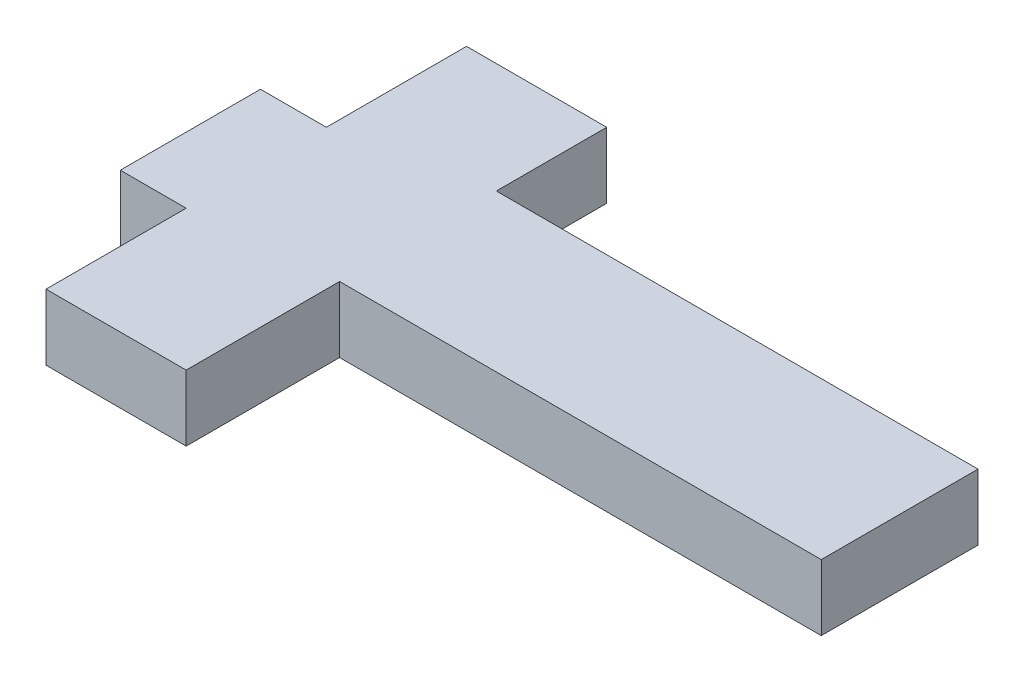
SolidWorks part; units mm, degrees
ref_plane "Front Plane" through (0, 0, 0) normal (0, 0, 1) x (1, 0, 0)
ref_plane "Top Plane" through (0, 0, 0) normal (0, 1, 0) x (1, 0, 0)
ref_plane "Right Plane" through (0, 0, 0) normal (1, 0, 0) x (0, 0, -1)
sketch "Sketch1" plane through (0, 0, 0) normal (0, 1, 0) x (1, 0, 0)
  line L12 (0, 0) -> (12.7, 0)
  line L13 (12.7, 0) -> (12.7, 13.9)
  line L14 (12.7, 13.9) -> (18.669, 13.9)
  line L15 (18.669, 13.9) -> (18.669, 28.1)
  line L16 (18.669, 28.1) -> (12.7, 28.1)
  line L17 (12.7, 28.1) -> (12.7, 38.1)
  line L18 (12.7, 38.1) -> (0, 38.1)
  line L19 (0, 38.1) -> (0, 25.4)
  line L20 (0, 25.4) -> (-5.969, 25.4)
  line L21 (-5.969, 25.4) -> (-5.969, 12.7)
  line L22 (-5.969, 12.7) -> (0, 12.7)
  line L23 (0, 12.7) -> (0, 0)
  dimension "D1" = 5.969
  dimension "D2" = 10
  dimension "D3" = 14.2
  dimension "D4" = 13.9
  dimension "D5" = 24.638
extrude "Boss-Extrude1" add sketch "Sketch1" along normal blind 5.969
sketch "Sketch2" plane through (0, 0, 0) normal (0, -1, 0) x (1, 0, 0)
  line L1 (18.669, -28.1) -> (56.338, -28.1)
  line L2 (18.669, -28.1) -> (18.669, -13.9)
  line L3 (18.669, -13.9) -> (56.338, -13.9)
  line L4 (56.338, -28.1) -> (56.338, -13.9)
  line L5 (18.669, -28.1) -> (56.338, -13.9) construction
  line L6 (18.669, -13.9) -> (56.338, -28.1) construction
  point P4 (37.5035, -21)
  dimension "D1" = 37.669
extrude "Boss-Extrude2" add sketch "Sketch2" against normal up to surface (5.969 mm away) up to face at (6.35, 5.969, -19.7)
